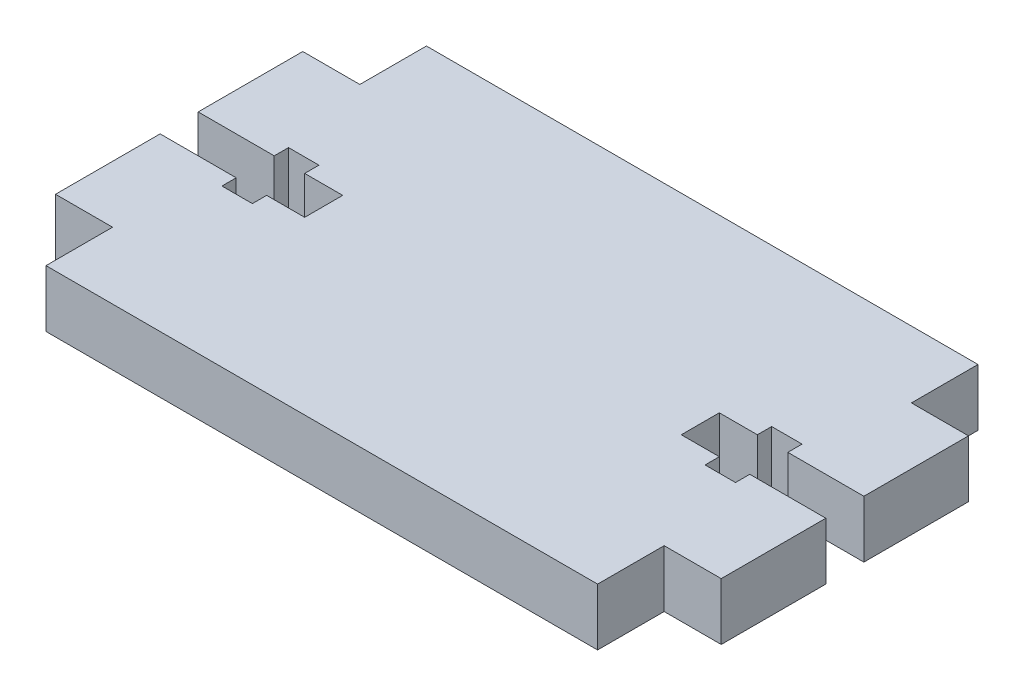
SolidWorks part; units mm, degrees
ref_plane "Front Plane" through (0, 0, 0) normal (0, 0, 1) x (1, 0, 0)
ref_plane "Top Plane" through (0, 0, 0) normal (0, 1, 0) x (1, 0, 0)
ref_plane "Right Plane" through (0, 0, 0) normal (1, 0, 0) x (0, 0, -1)
sketch "Sketch1" plane through (0, 0, 0) normal (0, 1, 0) x (1, 0, 0)
  line L0 (-29, -20) -> (-29, -13) construction
  line L1 (-29, 20) -> (29, 20)
  line L2 (-29, 20) -> (-29, 13)
  line L3 (-29, -20) -> (29, -20)
  line L4 (29, 20) -> (29, 13)
  line L5 (-29, 20) -> (29, -20) construction
  line L6 (-29, -20) -> (29, 20) construction
  line L7 (-29, -13) -> (-35, -13)
  line L8 (-35, -13) -> (-35, -2)
  line L9 (-35, 13) -> (-29, 13)
  line L10 (0, 20) -> (0, -20) construction
  line L11 (-29, -13) -> (-29, -20)
  line L12 (29, -13) -> (35, -13)
  line L13 (35, -13) -> (35, -2)
  line L14 (35, 13) -> (29, 13)
  line L15 (29, -13) -> (29, -20)
  line L16 (-35, 13) -> (-35, 2) construction
  line L17 (-35, 2) -> (-27, 2)
  line L18 (-27, 2) -> (-27, 3.5)
  line L19 (-27, 3.5) -> (-23.8, 3.5)
  line L20 (-23.8, 3.5) -> (-23.8, 2)
  line L21 (-23.8, 2) -> (-19.8, 2)
  line L22 (-19.8, 2) -> (-19.8, -2)
  line L23 (-19.8, -2) -> (-23.8, -2)
  line L24 (-23.8, -2) -> (-23.8, -3.5)
  line L25 (-23.8, -3.5) -> (-27, -3.5)
  line L26 (-27, -3.5) -> (-27, -2)
  line L27 (-27, -2) -> (-35, -2)
  line L28 (-35, 0) -> (35, 0) construction
  line L29 (27, -3.5) -> (27, -2)
  line L30 (23.8, -2) -> (23.8, -3.5)
  line L31 (27, -2) -> (35, -2)
  line L32 (23.8, -3.5) -> (27, -3.5)
  line L33 (19.8, -2) -> (23.8, -2)
  line L34 (19.8, 2) -> (19.8, -2)
  line L35 (23.8, 2) -> (19.8, 2)
  line L36 (23.8, 3.5) -> (23.8, 2)
  line L37 (27, 3.5) -> (23.8, 3.5)
  line L38 (27, 2) -> (27, 3.5)
  line L39 (35, 2) -> (27, 2)
  line L40 (-35, 2) -> (-35, 13)
  line L41 (35, 2) -> (35, 13)
  line L43 (-10, 9.5) -> (10, 9.5) construction
  line L44 (-10, 9.5) -> (-10, -9.5) construction
  line L45 (-10, -9.5) -> (10, -9.5) construction
  line L46 (10, 9.5) -> (10, -9.5) construction
  line L47 (-10, 9.5) -> (10, -9.5) construction
  line L48 (-10, -9.5) -> (10, 9.5) construction
  point P0 (0, 0)
  point P42 (0, 0)
  dimension "D1" = 7
  dimension "D2" = 26
  dimension "D3" = 6
  dimension "D4" = 11
extrude "Boss-Extrude1" add sketch "Sketch1" along normal blind 6
